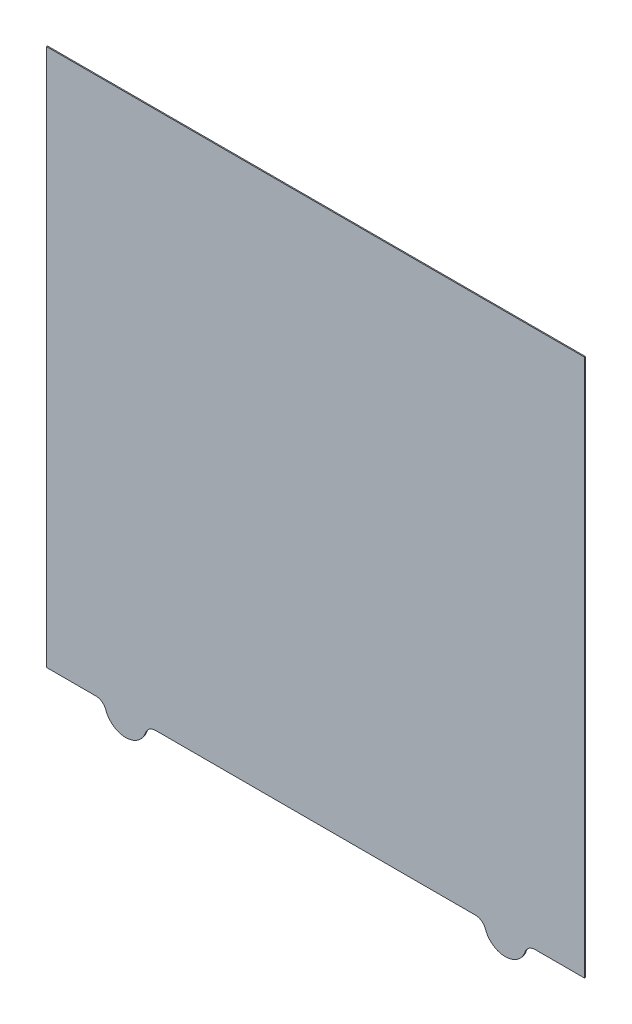
SolidWorks part; units mm, degrees
ref_plane "Front Plane" through (0, 0, 0) normal (0, 0, 1) x (1, 0, 0)
ref_plane "Top Plane" through (0, 0, 0) normal (0, 1, 0) x (1, 0, 0)
ref_plane "Right Plane" through (0, 0, 0) normal (1, 0, 0) x (0, 0, -1)
sketch "Sketch1" plane through (0, 0, 0) normal (0, 0, 1) x (1, 0, 0)
  line L0 (208.2843, -255) -> (255, -255)
  line L1 (-255, -255) -> (-208.2843, -255)
  line L2 (-255, -255) -> (-255, 255)
  line L3 (-255, 255) -> (255, 255)
  line L4 (255, -255) -> (255, 255)
  line L5 (-255, -255) -> (255, 255) construction
  line L6 (-255, 255) -> (255, -255) construction
  line L7 (-151.7157, -255) -> (151.7157, -255)
  arc A0 (-198.8562, -261.6667) -> (-161.1438, -261.6667) centre (-180, -255) ccw
  arc A1 (161.1438, -261.6667) -> (198.8562, -261.6667) centre (180, -255) ccw
  arc A2 (-198.8562, -261.6667) -> (-208.2843, -255) centre (-208.2843, -265) ccw
  arc A3 (-161.1438, -261.6667) -> (-151.7157, -255) centre (-151.7157, -265) cw
  arc A4 (161.1438, -261.6667) -> (151.7157, -255) centre (151.7157, -265) ccw
  arc A5 (198.8562, -261.6667) -> (208.2843, -255) centre (208.2843, -265) cw
  point P0 (0, 0)
  point P16 (-160, -255)
  point P21 (200, -255)
  dimension "D3" = 75
  dimension "D5" = 10
  dimension "D6" = 10
  dimension "D1" = 510
  dimension "D2" = 510
  dimension "D4" = 75
extrude "Boss-Extrude1" add sketch "Sketch1" along normal blind 1
